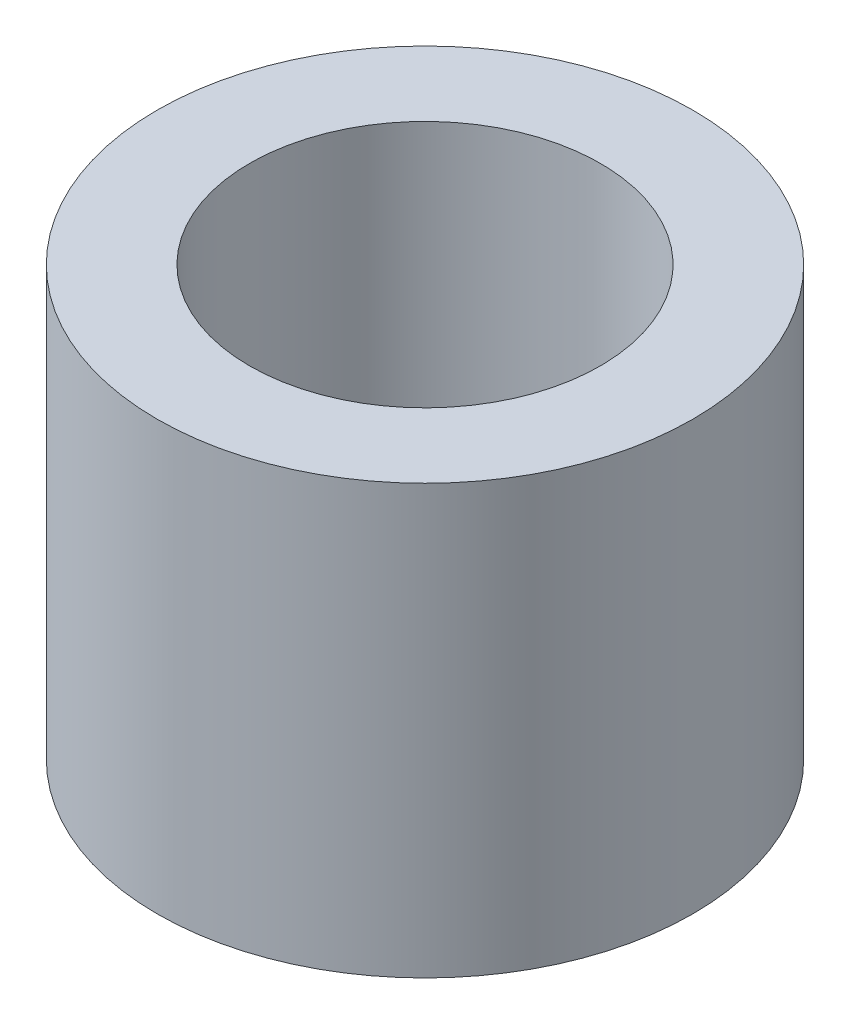
SolidWorks part; units mm, degrees
material "Nylon 6/10"
ref_plane "Front Plane" through (0, 0, 0) normal (0, 0, 1) x (1, 0, 0)
ref_plane "Top Plane" through (0, 0, 0) normal (0, 1, 0) x (1, 0, 0)
ref_plane "Right Plane" through (0, 0, 0) normal (1, 0, 0) x (0, 0, -1)
sketch "Sketch1" plane through (0, 0, 0) normal (0, 1, 0) x (1, 0, 0)
  circle A0 centre (0, 0) radius 3.9688
  circle A1 centre (0, 0) radius 2.6
  dimension "D1" = 5.2
  dimension "D2" = 7.9375
extrude "Boss-Extrude1" add sketch "Sketch1" along normal blind 6.35
